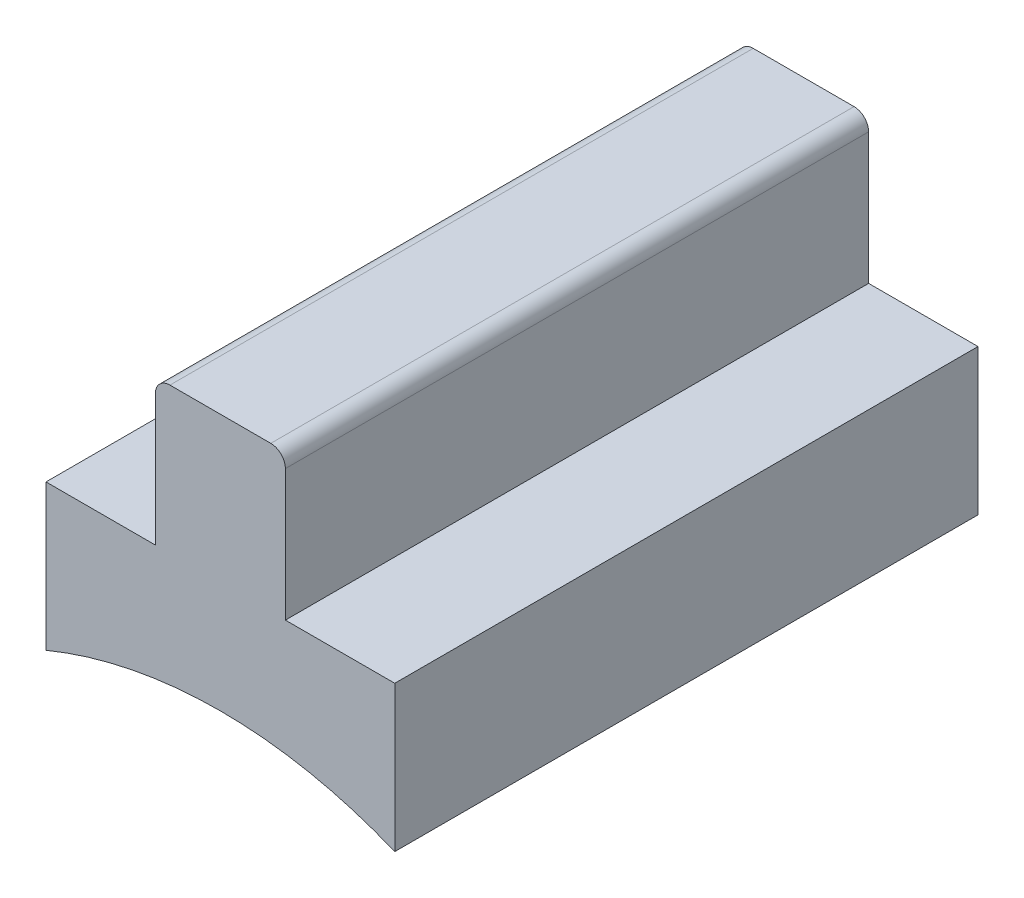
SolidWorks part; units mm, degrees
ref_plane "Front Plane" through (0, 0, 0) normal (0, 0, 1) x (1, 0, 0)
ref_plane "Top Plane" through (0, 0, 0) normal (0, 1, 0) x (1, 0, 0)
ref_plane "Right Plane" through (0, 0, 0) normal (1, 0, 0) x (0, 0, -1)
sketch "Sketch1" plane through (0, 0, 0) normal (0, 0, 1) x (1, 0, 0)
  line L3 (0, 0) -> (30.3755, 73.3329) construction
  line L4 (0, 0) -> (-30.3755, 73.3329) construction
  line L8 (-30.3755, 98.7329) -> (-11.3255, 98.7329)
  line L10 (-30.3755, 73.3329) -> (-30.3755, 98.7329)
  line L11 (-8.7855, 124.1329) -> (8.7855, 124.1329)
  line L12 (30.3755, 73.3329) -> (30.3755, 98.7329)
  line L13 (-11.3255, 98.7329) -> (-11.3255, 121.5929)
  line L14 (30.3755, 98.7329) -> (11.3255, 98.7329)
  line L15 (11.3255, 98.7329) -> (11.3255, 121.5929)
  arc A0 (30.3755, 73.3329) -> (-30.3755, 73.3329) centre (0, 0) ccw
  arc A1 (11.3255, 121.5929) -> (8.7855, 124.1329) centre (8.7855, 121.5929) ccw
  arc A2 (-11.3255, 121.5929) -> (-8.7855, 124.1329) centre (-8.7855, 121.5929) cw
  point P14 (-11.3255, 124.1329)
  dimension "D1" = 45
  dimension "D3" = 79.375
  dimension "D7" = 2.54
  dimension "D2" = 60.751
  dimension "D4" = 19.05
  dimension "D5" = 25.4
  dimension "D6" = 25.4
extrude "Boss-Extrude2" add sketch "Sketch1" along normal blind 101.6
